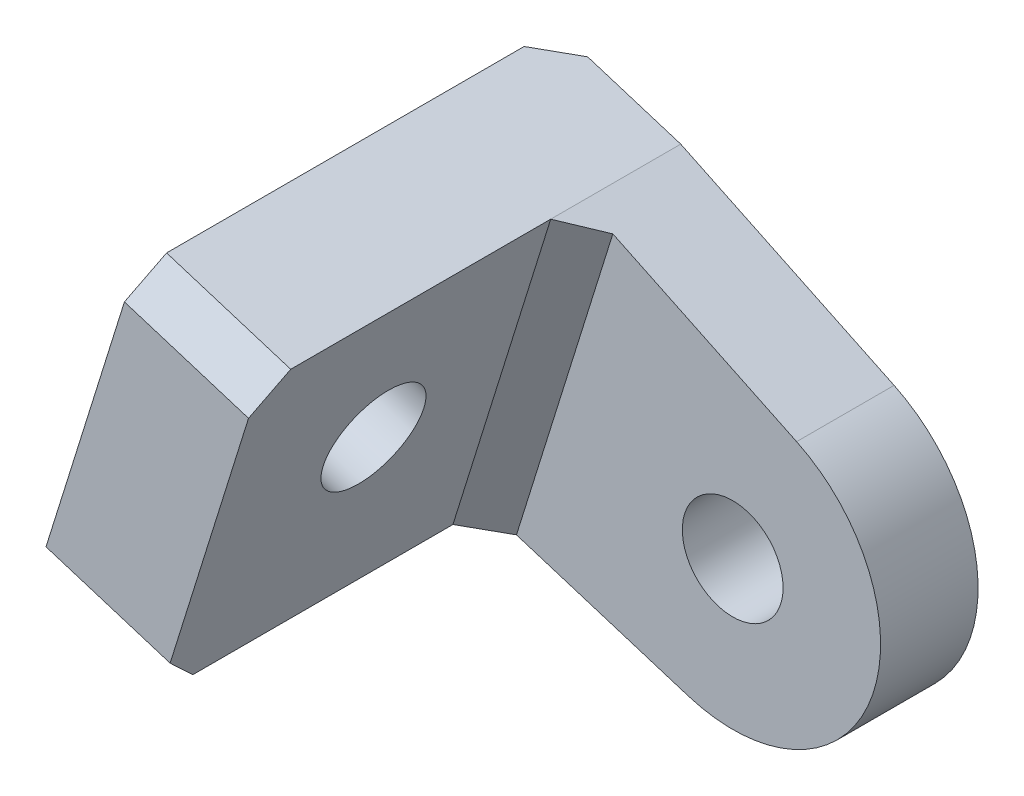
SolidWorks part; units mm, degrees
ref_plane "Front Plane" through (0, 0, 0) normal (0, 0, 1) x (1, 0, 0)
ref_plane "Top Plane" through (0, 0, 0) normal (0, 1, 0) x (1, 0, 0)
ref_plane "Right Plane" through (0, 0, 0) normal (1, 0, 0) x (0, 0, -1)
sketch "Sketch1" plane through (0, 0, 0) normal (0, 0, 1) x (1, 0, 0)
  line L0 (4.5872, 32.0905) -> (13.1786, 29.4093) construction
  line L1 (4.5872, 32.0905) -> (13.1786, 29.4093)
  line L2 (4.5872, 32.0905) -> (1.3298, 21.6525)
  line L3 (7.2749, 23.9188) -> (2.9315, 25.2743) construction
  line L4 (2.9315, 25.2743) -> (0.0677, 26.168) construction
  line L5 (7.2749, 23.9188) -> (8.6304, 28.2622) construction
  line L6 (8.6304, 28.2622) -> (-1.4406, 31.4051)
  line L7 (0.0677, 26.168) -> (-2.7961, 27.0617) construction
  line L8 (-2.7961, 27.0617) -> (-1.4406, 31.4051)
  line L9 (7.2749, 23.9188) -> (5.9194, 19.5754) construction
  line L10 (5.9194, 19.5754) -> (-4.1516, 22.7183)
  line L11 (-2.7961, 27.0617) -> (-4.1516, 22.7183)
  line L12 (-1.4406, 31.4051) -> (-1.1427, 32.3597)
  line L13 (-1.1427, 32.3597) -> (2.6757, 31.1681)
  line L14 (2.6757, 31.1681) -> (2.3777, 30.2135)
  line L15 (2.6757, 31.1681) -> (9.2411, 28.022)
  circle A0 centre (7.2749, 23.9188) radius 1.55
  circle A1 centre (7.2749, 23.9188) radius 4.55
  dimension "D1" = 3.1
  dimension "D2" = 9.1
  dimension "D3" = 3
  dimension "D4" = 3
  dimension "D5" = 1
  dimension "D6" = 4
extrude "Boss-Extrude1" add sketch "Sketch1" along normal blind 3
sketch "Sketch2" plane through (0, 0, 3) normal (0, 0, 1) x (1, 0, 0)
  line L0 (-1.1427, 32.3597) -> (-4.1516, 22.7183)
  line L1 (-4.1516, 22.7183) -> (-0.3332, 21.5267)
  line L2 (5.9194, 19.5754) -> (-4.1516, 22.7183) construction
  line L3 (-0.3332, 21.5267) -> (2.6757, 31.1681)
  line L5 (-1.1427, 32.3597) -> (2.6757, 31.1681)
  dimension "D1" = 4
extrude "Boss-Extrude2" add sketch "Sketch2" along normal blind 10
sketch "Sketch3" plane through (-10.2437, 3.1968, 0) normal (-0.9546, 0.2979, 0) x (0, 0, 1)
  ellipse E0 centre (8.0559, 25.8577) end of major axis (6.5059, 25.8577) minor radius 1.55 construction
  ellipse E1 centre (8.0559, 25.8577) end of major axis (6.5059, 25.8577) minor radius 1.55
extrude "Cut-Extrude1" cut sketch "Sketch3" against normal up to next
chamfer "Chamfer1" distance 1 angle 45 2 edges at (-2.2424, 22.1225, 13) (0.7665, 31.7639, 13)
chamfer "Chamfer2" distance 1 angle 45 1 edges
chamfer "Chamfer3" distance 1 angle 45 1 edges at (-2.6471, 27.539, 0)
